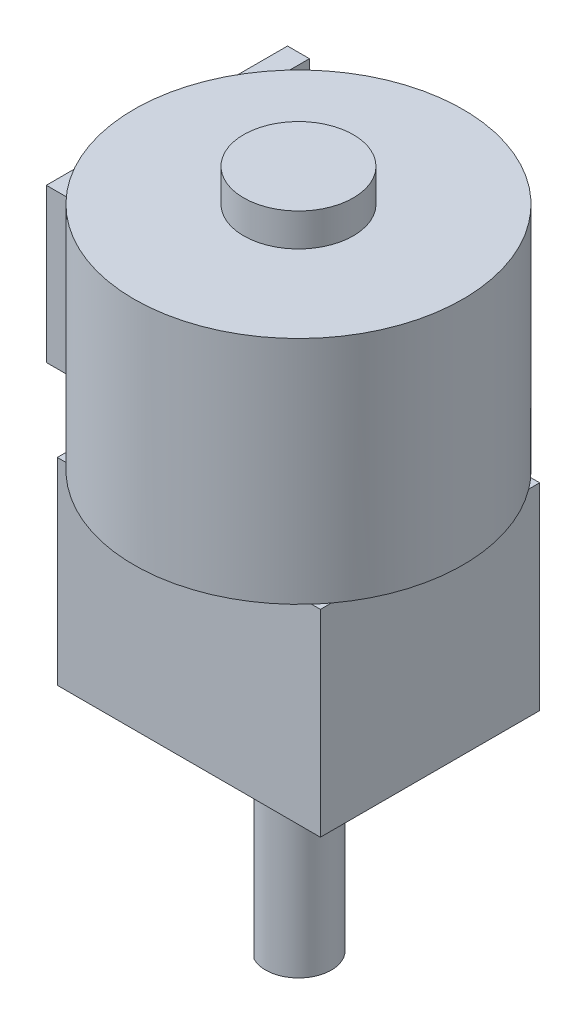
SolidWorks part; units mm, degrees
ref_plane "Front Plane" through (0, 0, 0) normal (0, 0, 1) x (1, 0, 0)
ref_plane "Top Plane" through (0, 0, 0) normal (0, 1, 0) x (1, 0, 0)
ref_plane "Right Plane" through (0, 0, 0) normal (1, 0, 0) x (0, 0, -1)
sketch "Sketch1" plane through (0, 0, 0) normal (0, 1, 0) x (1, 0, 0)
  line L1 (-6, 5) -> (6, 5)
  line L2 (-6, 5) -> (-6, -5)
  line L3 (-6, -5) -> (6, -5)
  line L4 (6, 5) -> (6, -5)
  line L5 (0, -5) -> (0, 5) construction
  line L6 (-6, 0) -> (6, 0) construction
  point P4 (0, 0)
  point P5 (0, 0)
  point P288 (0, 0)
  dimension "D1" = 12
  dimension "D2" = 10
extrude "Boss-Extrude1" add sketch "Sketch1" along normal blind 9
sketch "Sketch2" plane through (0, 0, 0) normal (0, -1, 0) x (1, 0, 0)
  circle A0 centre (0, 0) radius 2
  dimension "D1" = 4
extrude "Boss-Extrude2" add sketch "Sketch2" along normal blind 1
sketch "Sketch3" plane through (0, -1, 0) normal (0, -1, 0) x (-1, 0, 0)
  line L0 (0.7, 1.3266) -> (0.7, -1.3266)
  line L1 (0, 5.5) -> (0, -5.5) construction
  arc A0 (0.7, 1.3266) -> (0.7, -1.3266) centre (0, 0) ccw
  dimension "D1" = 3
  dimension "D2" = 0.7
extrude "Boss-Extrude3" add sketch "Sketch3" along normal blind 9
hole_wizard "M1.6 Clearance Hole1" positions "Sketch4" profile "Sketch5" hole size "M1.6" standard "ISO"
sketch "Sketch4" plane through (0, 0, 0) normal (0, -1, 0) x (-1, 0, 0)
  line L0 (-6.6, 0) -> (6.6, 0) construction
  line L1 (0, 5.5) -> (0, -5.5) construction
  point P0 (4.5, 0)
  point P5 (0, 0)
  point P6 (0, 0)
  point P11 (-4.5, 0)
  dimension "D1" = 4.5
sketch "Sketch5" plane through (-4.5, 0, 0) normal (1, 0, 0) x (0, 0, -1)
  line L0 (0, 0) -> (0, 2.5408)
  line L1 (0, 2.5408) -> (0.9, 2)
  line L2 (0.9, 2) -> (0.9, 0)
  line L5 (0.9, 0) -> (0, 0)
  line L10 (0, 2.5408) -> (-0.9, 2) construction
  line L11 (0, -6.35) -> (0, 107.95) construction
  dimension "Hole Dia." = 1.8
  dimension "Hole Depth" = 2
  dimension "Drill Angle" = 118
sketch "Sketch6" plane through (0, 9, 0) normal (0, 1, 0) x (1, 0, 0)
  circle A0 centre (0, 0) radius 7.5
  dimension "D1" = 15
extrude "Boss-Extrude4" add sketch "Sketch6" along normal blind 10.5
sketch "Sketch7" plane through (0, 19.5, 0) normal (0, 1, 0) x (1, 0, 0)
  circle A0 centre (0, 0) radius 2.5
  dimension "D1" = 5
extrude "Boss-Extrude5" add sketch "Sketch7" along normal blind 1.5
ref_plane "Plane1" through (0, 14, 0) normal (0, 1, 0) x (1, 0, 0)
sketch "Sketch8" plane through (0, 14, 0) normal (0, 1, 0) x (1, 0, 0)
  line L1 (-8.5, -3) -> (-7.5, -3)
  line L2 (-8.5, -3) -> (-8.5, 8)
  line L3 (-8.5, 8) -> (-7.5, 8)
  line L4 (-7.5, -3) -> (-7.5, 8)
  line L5 (-8.25, 0) -> (8.25, 0) construction
  circle A0 centre (0, 0) radius 7.5 construction
  point P244 (-10.5222, 0)
  dimension "D1" = 11
  dimension "D2" = 3
  dimension "D3" = 1
extrude "Boss-Extrude6" add sketch "Sketch8" along normal mid plane 7 separate body
